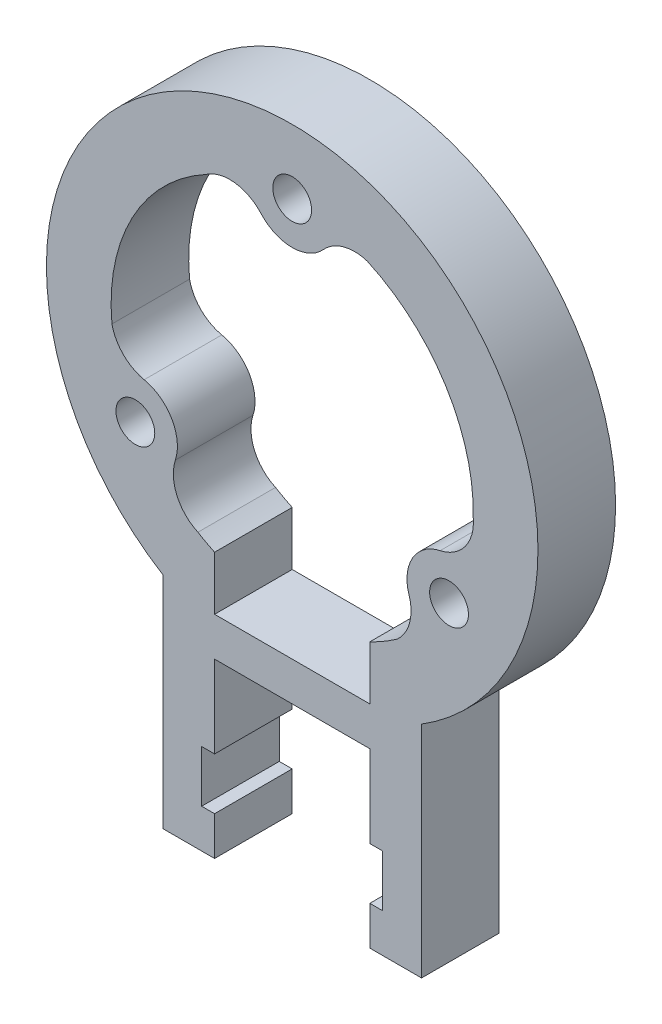
SolidWorks part; units mm, degrees
ref_plane "Plan de face" through (0, 0, 0) normal (0, 0, 1) x (1, 0, 0)
ref_plane "Plan de dessus" through (0, 0, 0) normal (0, 1, 0) x (1, 0, 0)
ref_plane "Plan de droite" through (0, 0, 0) normal (1, 0, 0) x (0, 0, -1)
sketch "Esquisse1" plane through (0, 0, 0) normal (0, 0, 1) x (1, 0, 0)
  line L0 (0, 14) -> (-12.125, -7.0011) construction
  line L1 (-12.125, -7.0011) -> (-10.6244, -7.0011) construction
  line L2 (12.125, -7.0011) -> (0, 14) construction
  line L3 (-6, -33.1555) -> (-6, -30.1555)
  line L5 (10, -16.1555) -> (10, -33.1555)
  line L6 (10, -33.1555) -> (6, -33.1555)
  line L7 (-10, -16.1555) -> (-10, -33.1555)
  line L8 (-7, -26.1555) -> (-6, -26.1555)
  line L9 (-7, -26.1555) -> (-7, -30.1555)
  line L10 (-7, -30.1555) -> (-6, -30.1555)
  line L11 (7, -26.1555) -> (7, -30.1555)
  line L12 (6, -33.1555) -> (6, -30.1555)
  line L13 (10, -7.0011) -> (12.125, -7.0011) construction
  line L14 (-6, -33.1555) -> (-10, -33.1555)
  line L15 (6, -30.1555) -> (7, -30.1555)
  line L16 (6, -26.1555) -> (7, -26.1555)
  line L17 (-6, -26.1555) -> (-6, -19.8055)
  line L18 (6, -26.1555) -> (6, -19.8055)
  line L19 (6, -19.8055) -> (-6, -19.8055)
  line L20 (6, -16.8055) -> (-6, -16.8055)
  line L21 (6, -16.8055) -> (6, -12.6491)
  line L22 (-6, -16.8055) -> (-6, -12.6491)
  arc A0 (10, -16.1555) -> (-10, -16.1555) centre (0, 0) ccw
  circle A2 centre (0, 14) radius 1.5
  arc A12 (-2.411, 11.8207) -> (2.411, 11.8207) centre (0, 14) ccw
  arc A16 (5.8094, 12.7378) -> (2.411, 11.8207) centre (4.8221, 9.6414) ccw
  arc A17 (-2.411, 11.8207) -> (-6.7074, 12.2887) centre (-4.8221, 9.6414) ccw
  arc A18 (-6.7074, 12.2887) -> (-13.9359, -1.3378) centre (0, 0) ccw
  arc A19 (8.1265, -11.4) -> (9.0315, -7.9984) centre (5.9386, -8.9967) ccw
  arc A20 (11.4425, -3.8223) -> (9.0315, -7.9984) centre (12.1244, -7) ccw
  arc A21 (11.4425, -3.8223) -> (13.996, -0.3356) centre (10.7607, -0.6447) ccw
  circle A22 centre (12.1244, -7) radius 1.5
  arc A23 (-13.9359, -1.3378) -> (-11.4425, -3.8223) centre (-10.7607, -0.6447) ccw
  arc A24 (-9.0315, -7.9984) -> (-11.4425, -3.8223) centre (-12.1244, -7) ccw
  arc A25 (-9.0315, -7.9984) -> (-7.2886, -11.9531) centre (-5.9386, -8.9967) ccw
  circle A26 centre (-12.1244, -7) radius 1.5
  arc A27 (-7.2886, -11.9531) -> (-6, -12.6491) centre (0, 0) ccw
  arc A28 (13.996, -0.3356) -> (5.8094, 12.7378) centre (0, 0) ccw
  circle A29 centre (0, 14) radius 3.25 construction
  arc A30 (6, -12.6491) -> (8.1265, -11.4) centre (0, 0) ccw
  point P31 (0, 0)
  point P35 (-10, -16.1555)
  point P36 (10, -16.1555)
  point P45 (6, -19.8055)
  point P46 (6, -33.1555)
  point P49 (-6, -33.1555)
  point P55 (6, -16.8055)
  dimension "D1" = 38
  dimension "D2" = 3
  dimension "D3" = 3
  dimension "D4" = 6.5
  dimension "D5" = 14
  dimension "D8" = 14
  dimension "D9" = 3.25
  dimension "D10" = 14
  dimension "D11" = 3.25
  dimension "D12" = 24.25
  dimension "D13" = 24.25
  dimension "D16" = 20
  dimension "D6" = 60
  dimension "D7" = 60
  dimension "D14" = 10.78
  dimension "D15" = 10.78
  dimension "D17" = 2.125
  dimension "D18" = 10
  dimension "D19" = 4
  dimension "D20" = 3
  dimension "D21" = 3
  dimension "D22" = 3
  dimension "D23" = 13.35
  dimension "D24" = 3
  dimension "D25" = 4
  dimension "D26" = 4
extrude "Boss.-Extru.2" add sketch "Esquisse1" along normal blind 6
